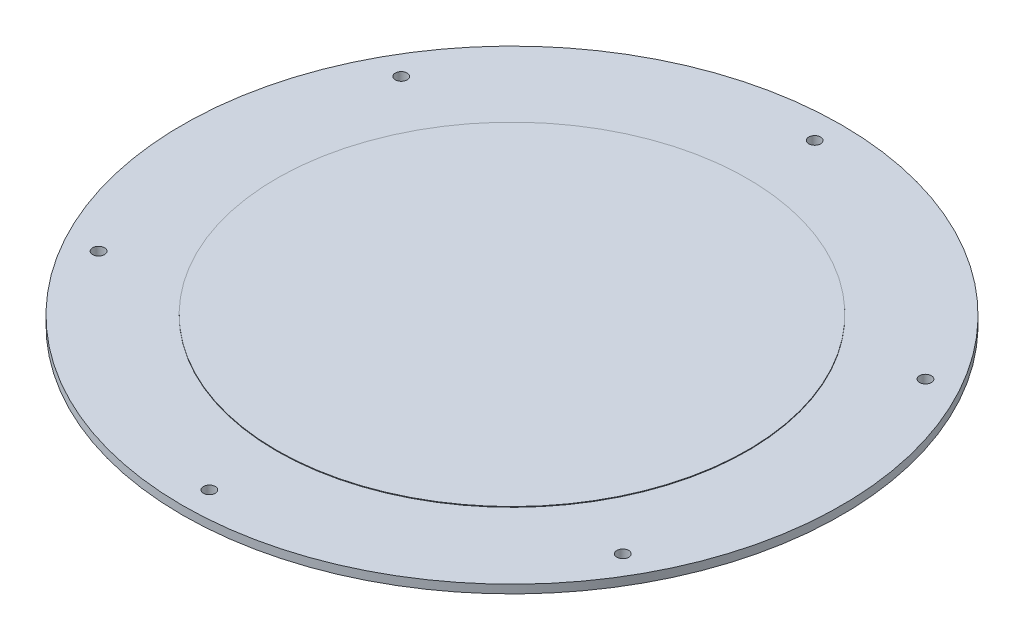
SolidWorks part; units mm, degrees
material "PVC Rigid"
ref_plane "Front Plane" through (0, 0, 0) normal (0, 0, 1) x (1, 0, 0)
ref_plane "Top Plane" through (0, 0, 0) normal (0, 1, 0) x (1, 0, 0)
ref_plane "Right Plane" through (0, 0, 0) normal (1, 0, 0) x (0, 0, -1)
sketch "Sketch1" plane through (0, 0, 0) normal (1, 0, 0) x (0, 0, -1)
  line L0 (89.535, 0) -> (92.71, 0)
  line L1 (92.71, 0) -> (92.71, 9.525)
  line L2 (92.71, 9.525) -> (124.46, 9.525)
  line L3 (124.46, 9.525) -> (124.46, 12.7)
  line L4 (124.46, 12.7) -> (0, 12.7)
  line L5 (0, 12.7) -> (0, 9.525)
  line L6 (0, 9.525) -> (89.535, 9.525)
  line L7 (89.535, 9.525) -> (89.535, 0)
  line L8 (0, 0) -> (0, 12.7) construction
  dimension "D1" = 12.7
  dimension "D2" = 3.175
  dimension "D3" = 92.71
  dimension "D4" = 124.46
  dimension "D5" = 3.175
  dimension "D6" = 12.7
revolve "Revolve1" add sketch "Sketch1" angle 360 about L8
hole_wizard "#8 Clearance Hole1" positions "Sketch2" profile "Sketch3" hole size "#8" standard "ANSI Inch" end condition up to next
sketch "Sketch2" plane through (0, 12.7, 0) normal (0, 1, 0) x (1, 0, 0)
  line L1 (0, 114.3) -> (-98.9867, 57.15)
  line L2 (-98.9867, 57.15) -> (-98.9867, -57.15)
  line L3 (-98.9867, -57.15) -> (0, -114.3)
  line L4 (0, -114.3) -> (98.9867, -57.15)
  line L5 (98.9867, -57.15) -> (98.9867, 57.15)
  line L6 (98.9867, 57.15) -> (0, 114.3)
  circle A1 centre (0, 0) radius 98.9867 construction
  point P0 (0, 114.3)
  dimension "D1" = 114.3
sketch "Sketch3" plane through (0, 12.7, -114.3) normal (1, 0, 0) x (0, 0, 1)
  line L0 (0, 0) -> (0, 3.176)
  line L1 (0, 3.176) -> (2.2479, 3.176)
  line L2 (2.2479, 3.176) -> (2.2479, 0)
  line L5 (2.2479, 0) -> (0, 0)
  line L11 (0, -6.35) -> (0, 107.95) construction
  dimension "Thru Hole Dia." = 4.4958
  dimension "Thru Hole Depth" = 3.176
pattern_circular "CirPattern1" count 6 over 360 about axis through (0, 0, 0) along (0, 1, 0) of "#8 Clearance Hole1"
sketch "Sketch4" plane through (0, 12.7, 0) normal (0, 1, 0) x (1, 0, 0)
  circle A0 centre (0, 0) radius 88.9
  dimension "D1" = 177.8
extrude "Cut-Extrude1" cut sketch "Sketch4" against normal through all
sketch "Sketch5" plane through (0, 12.7, 0) normal (0, 1, 0) x (1, 0, 0)
  circle A0 centre (0, 0) radius 88.9 construction
  circle A1 centre (0, 0) radius 88.9
extrude "Boss-Extrude2" add sketch "Sketch5" against normal blind 2.54 from offset 0.254 contours A1
